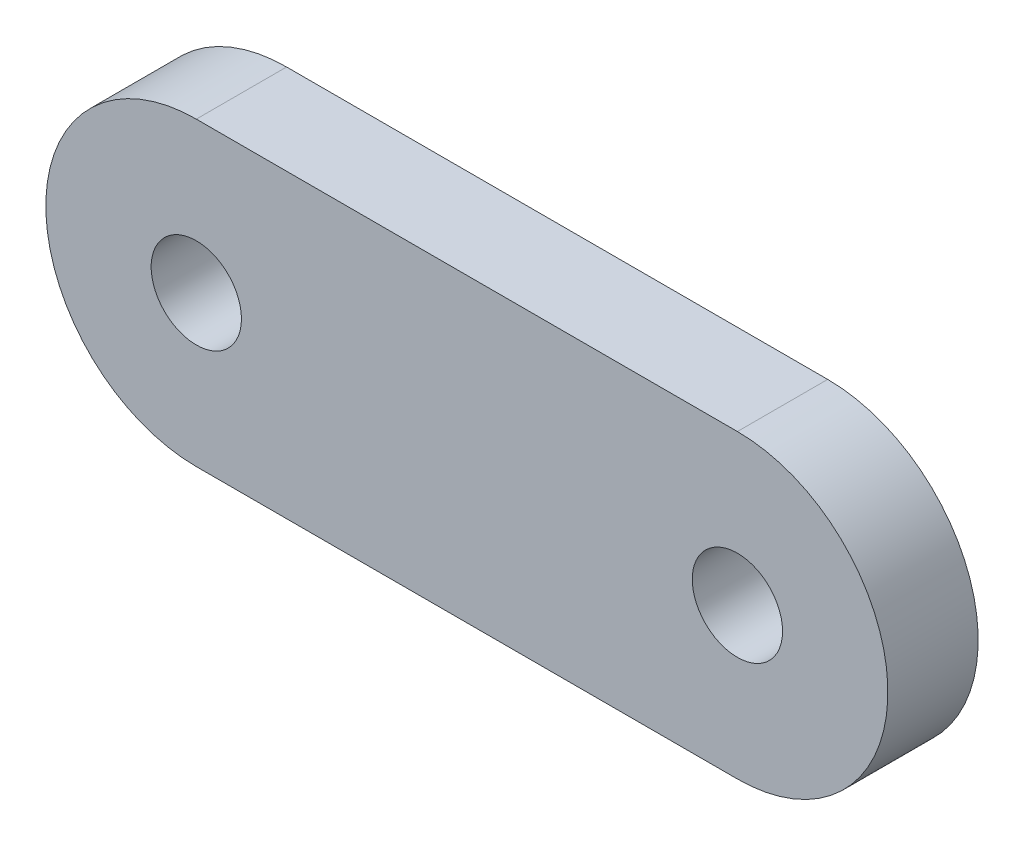
SolidWorks part; units mm, degrees
ref_plane "前基準面" through (0, 0, 0) normal (0, 0, 1) x (1, 0, 0)
ref_plane "上基準面" through (0, 0, 0) normal (0, 1, 0) x (1, 0, 0)
ref_plane "右基準面" through (0, 0, 0) normal (1, 0, 0) x (0, 0, -1)
sketch "草圖1" plane through (0, 0, 0) normal (0, 0, 1) x (1, 0, 0)
  line L0 (-4.495, 0) -> (4.495, 0) construction
  line L1 (-4.495, 2.5) -> (4.495, 2.5)
  line L2 (-4.495, -2.5) -> (4.495, -2.5)
  arc A0 (-4.495, 2.5) -> (-4.495, -2.5) centre (-4.495, 0) ccw
  arc A1 (4.495, -2.5) -> (4.495, 2.5) centre (4.495, 0) ccw
  circle A2 centre (4.495, 0) radius 0.75
  circle A3 centre (-4.495, 0) radius 0.75
  point P3 (0, 0)
  dimension "D2" = 2.5
  dimension "D3" = 1.5
  dimension "D1" = 8.99
extrude "填料-伸長1" add sketch "草圖1" along normal mid plane 1.5
